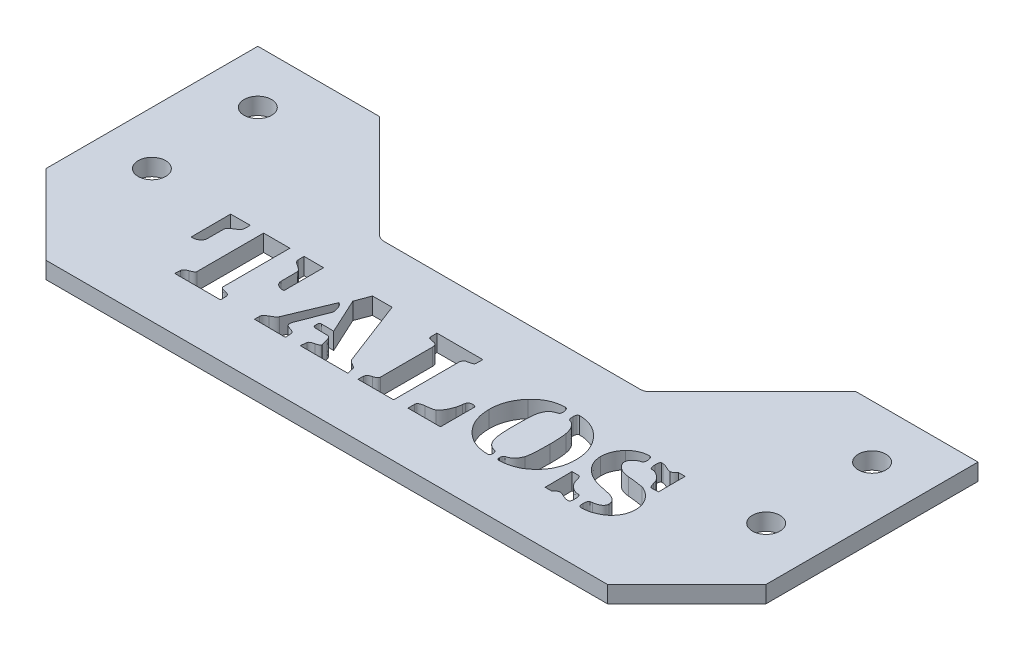
SolidWorks part; units mm, degrees
material "6061-T6 (SS)"
ref_plane "Front Plane" through (0, 0, 0) normal (0, 0, 1) x (1, 0, 0)
ref_plane "Top Plane" through (0, 0, 0) normal (0, 1, 0) x (1, 0, 0)
ref_plane "Right Plane" through (0, 0, 0) normal (1, 0, 0) x (0, 0, -1)
sketch "Sketch1" plane through (0, 0, 0) normal (0, 1, 0) x (1, 0, 0)
  line L0 (-48, 40) -> (-48, 30)
  line L1 (68, 0) -> (-68, 0)
  line L2 (68, 40) -> (68, 0)
  line L3 (48, 40) -> (68, 40)
  line L4 (48, 40) -> (48, 30)
  line L5 (48, 30) -> (38, 20)
  line L8 (-38, 20) -> (38, 20)
  line L9 (-58, 40) -> (-58, 0) construction
  line L10 (-68, 20) -> (0, 20) construction
  line L13 (0, 0) -> (0, 20) construction
  line L14 (-48, 40) -> (-68, 40)
  line L15 (-68, 40) -> (-68, 0)
  line L16 (-48, 30) -> (-38, 20)
  line L19 (-38, 20) -> (0, 20) construction
  circle A0 centre (-58, 10) radius 2.6
  circle A1 centre (-58, 30) radius 2.6
  circle A3 centre (58, 10) radius 2.6
  circle A4 centre (58, 30) radius 2.6
  dimension "D4" = 20
  dimension "D5" = 5.2
  dimension "D2" = 40
  dimension "D3" = 20
  dimension "D6" = 136
  dimension "D8" = 10
extrude "Boss-Extrude1" add sketch "Sketch1" along normal blind 3.175
sketch "Sketch2" plane through (0, 3.175, 0) normal (0, 1, 0) x (1, 0, 0)
  line L0 (-58, 10) -> (-58, -5) construction
  line L1 (-58, -5) -> (58, -5) construction
  line L2 (58, -5) -> (58, 10) construction
  text T0 "TALOS" font "Lintsec" height 15
  dimension "D1" = 15
sketch "Sketch3" plane through (0, 3.175, 0) normal (0, 1, 0) x (1, 0, 0)
  line L0 (-68, 0) -> (-53, -15)
  line L1 (-53, -15) -> (53, -15)
  line L2 (0, 0) -> (0, -15) construction
  line L5 (-38, 20) -> (-48, 30) construction
  line L6 (-58, -5) -> (58, -5) construction
  line L7 (68, 0) -> (53, -15)
  line L8 (-68, 0) -> (68, 0) construction
  line L9 (-68, 0) -> (68, 0)
  dimension "D1" = 10
extrude "Boss-Extrude2" add sketch "Sketch3" against normal up to surface (3.175 mm away) up to face at (-58, 0, -7.4)
extrude "Cut-Extrude1" cut sketch "Sketch2" against normal up to surface (3.175 mm away) up to face at (-58, 0, -7.4)
sketch "Sketch4" plane through (0, 3.175, 0) normal (0, 1, 0) x (1, 0, 0)
  line L0 (-48, 40) -> (-48, 30)
  line L1 (-48, 30) -> (-38, 20)
  line L2 (-38, 20) -> (-28, 20)
  line L3 (38, 20) -> (-38, 20) construction
  line L4 (-48, 40) -> (-45, 40)
  line L5 (-45, 40) -> (-28, 23)
  line L6 (-28, 23) -> (-28, 20)
  line L7 (0, 20) -> (0, 0) construction
  line L9 (-28, 23) -> (-25.5858, 20.5858)
  line L10 (28, 20) -> (24.1716, 20)
  line L11 (-28, 20) -> (-24.1716, 20)
  line L12 (28, 23) -> (25.5858, 20.5858)
  line L13 (28, 23) -> (28, 20)
  line L14 (45, 40) -> (28, 23)
  line L15 (48, 40) -> (45, 40)
  line L16 (38, 20) -> (28, 20)
  line L17 (48, 30) -> (38, 20)
  line L18 (48, 40) -> (48, 30)
  arc A0 (-25.5858, 20.5858) -> (-24.1716, 20) centre (-24.1716, 22) ccw
  arc A1 (25.5858, 20.5858) -> (24.1716, 20) centre (24.1716, 22) cw
  dimension "D4" = 2
  dimension "D1" = 3
  dimension "D2" = 45
  dimension "D3" = 3
extrude "Boss-Extrude3" add sketch "Sketch4" against normal up to surface (3.175 mm away) up to face at (33.6533, 0, 3.2992)
